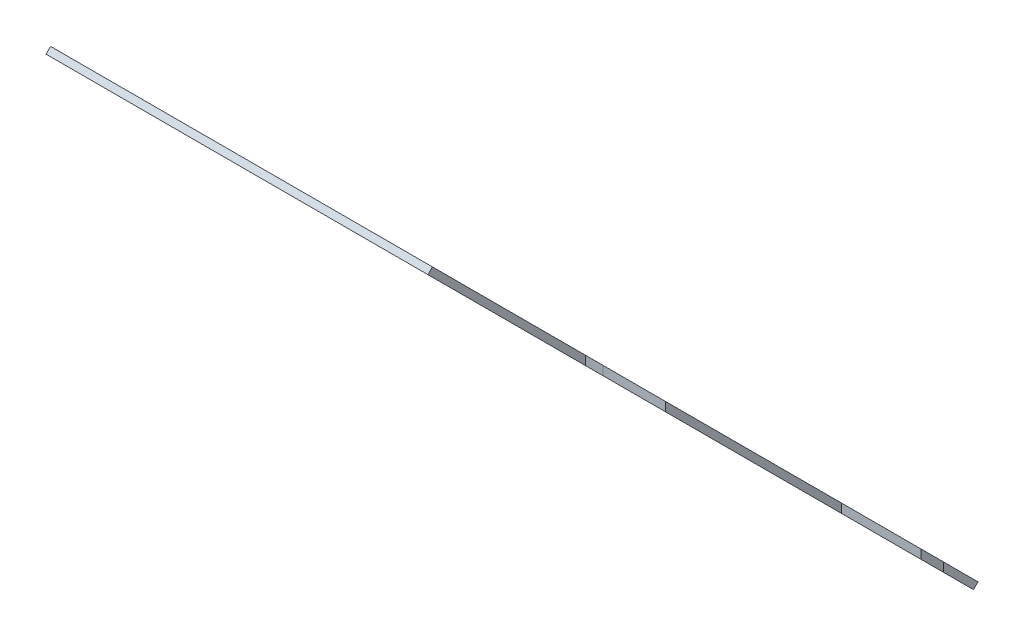
SolidWorks part; units mm, degrees
ref_plane "Plano frontal" through (0, 0, 0) normal (0, 0, 1) x (1, 0, 0)
ref_plane "Plano superior" through (0, 0, 0) normal (0, 1, 0) x (1, 0, 0)
ref_plane "Plano direito" through (0, 0, 0) normal (1, 0, 0) x (0, 0, -1)
sketch "Sketch3" plane through (0, 0, 0) normal (1, 0, 0) x (0, 0, -1)
  line L0 (-40199.9002, 3730.3647) -> (-40199.9002, 2810.9901) construction
  line L1 (-40199.9002, 12144.1489) -> (-40199.9002, -2855.8511) construction
  line L2 (-40199.9002, 2810.9901) -> (-41009.724, 3620.8139)
  line L3 (-41009.724, 3620.8139) -> (-41002.653, 3627.885)
  line L4 (-41002.653, 3627.885) -> (-40199.9002, 2825.1322)
  line L5 (-40199.9002, 2825.1322) -> (-40199.9002, 2810.9901)
  dimension "D1" = 10
  dimension "D2" = 45
extrude "Boss-Extrude1" add sketch "Sketch3" against normal blind 600 from surface at -22799.5611
sketch "Sketch4" plane through (0, 0, 0) normal (0, 1, 0) x (1, 0, 0)
  line L0 (-22799.5611, -40199.9002) -> (-22799.5611, -41002.653) construction
  line L1 (-22799.5611, -40360.1738) -> (-23030.5481, -40360.1738)
  line L2 (-22799.5611, -40360.1738) -> (-22799.5611, -40235.0266)
  line L3 (-22799.5611, -40235.0266) -> (-23030.5481, -40235.0266)
  line L5 (-22897.4106, -40699.3838) -> (-22959.9842, -40699.3838) construction
  line L6 (-22799.5611, -40761.9574) -> (-22897.4106, -40761.9574)
  line L7 (-22799.5611, -40761.9574) -> (-22799.5611, -40636.8102)
  line L8 (-22799.5611, -40636.8102) -> (-22897.4106, -40636.8102)
  line L10 (-23030.5481, -40297.6002) -> (-23093.1217, -40297.6002) construction
  line L11 (-22897.4106, -40761.9574) -> (-22897.4106, -40636.8102) construction
  line L12 (-23030.5481, -40360.1738) -> (-23030.5481, -40235.0266) construction
  line L13 (-22901.7025, -40699.3838) -> (-23026.1108, -40699.3838) construction
  arc A4 (-23030.5481, -40235.0266) -> (-23030.5481, -40360.1738) centre (-23030.5481, -40297.6002) ccw
  arc A5 (-22897.4106, -40636.8102) -> (-22897.4106, -40761.9574) centre (-22897.4106, -40699.3838) ccw
extrude "Cut-Extrude1" cut sketch "Sketch4" against normal up to vertex from vertex
sketch "Sketch5" plane through (-23399.5611, 0, 0) normal (-1, 0, 0) x (0, 0, 1)
  line L0 (40199.9002, 2810.9901) -> (40043.6383, 2654.7282)
  line L1 (40043.6383, 2654.7282) -> (40043.6383, 2668.8703)
  line L2 (40043.6383, 2668.8703) -> (40199.9002, 2825.1322)
  line L3 (40199.9002, 2825.1322) -> (40199.9002, 2810.9901)
  line L4 (40043.6383, 2668.8703) -> (40050.7093, 2661.7993)
  line M8 (40199.9002, 2825.1322) -> (40199.9002, 2810.9901)
extrude "Boss-Extrude2" add sketch "Sketch5" against normal up to surface (498 mm away) contours L2 L4 L0 M8
sketch "Sketch6" plane through (0, -18687.384, 18687.384) normal (0, 0.7071, -0.7071) x (1, 0, 0)
  line L0 (-23164.5611, -30416.8045) -> (-23359.5611, -30416.8045) construction
  line L1 (-23164.5611, -30426.8045) -> (-23359.5611, -30426.8045)
  line L2 (-23164.5611, -30406.8045) -> (-23359.5611, -30406.8045)
  line L3 (-23359.5611, -30416.8045) -> (-23359.5611, -31160.8045) construction
  line L4 (-23349.5611, -30416.8045) -> (-23349.5611, -31160.8045)
  line L5 (-23369.5611, -30416.8045) -> (-23369.5611, -31160.8045)
  line L6 (-23359.5611, -31160.8045) -> (-23039.5611, -31160.8045) construction
  line L7 (-23359.5611, -31150.8045) -> (-23039.5611, -31150.8045)
  line L8 (-23359.5611, -31170.8045) -> (-23039.5611, -31170.8045)
  line L9 (-23399.5611, -31558.5561) -> (-23399.5611, -30202.3045) construction
  line L11 (-23164.5611, -30596.8045) -> (-23359.5611, -30596.8045) construction
  line L12 (-23164.5611, -30606.8045) -> (-23359.5611, -30606.8045)
  line L13 (-23164.5611, -30586.8045) -> (-23359.5611, -30586.8045)
  line L14 (-23359.5611, -30980.8045) -> (-23039.5611, -30980.8045) construction
  line L15 (-23359.5611, -30970.8045) -> (-23039.5611, -30970.8045)
  line L16 (-23359.5611, -30990.8045) -> (-23039.5611, -30990.8045)
  line L17 (-22901.5611, -30202.3045) -> (-23399.5611, -30202.3045) construction
  arc A0 (-23164.5611, -30426.8045) -> (-23164.5611, -30406.8045) centre (-23164.5611, -30416.8045) ccw
  arc A1 (-23359.5611, -30406.8045) -> (-23359.5611, -30426.8045) centre (-23359.5611, -30416.8045) ccw
  arc A2 (-23349.5611, -30416.8045) -> (-23369.5611, -30416.8045) centre (-23359.5611, -30416.8045) ccw
  arc A3 (-23369.5611, -31160.8045) -> (-23349.5611, -31160.8045) centre (-23359.5611, -31160.8045) ccw
  arc A4 (-23359.5611, -31150.8045) -> (-23359.5611, -31170.8045) centre (-23359.5611, -31160.8045) ccw
  arc A5 (-23039.5611, -31170.8045) -> (-23039.5611, -31150.8045) centre (-23039.5611, -31160.8045) ccw
  arc A6 (-23164.5611, -30606.8045) -> (-23164.5611, -30586.8045) centre (-23164.5611, -30596.8045) ccw
  arc A7 (-23359.5611, -30586.8045) -> (-23359.5611, -30606.8045) centre (-23359.5611, -30596.8045) ccw
  arc A8 (-23359.5611, -30970.8045) -> (-23359.5611, -30990.8045) centre (-23359.5611, -30980.8045) ccw
  arc A9 (-23039.5611, -30990.8045) -> (-23039.5611, -30970.8045) centre (-23039.5611, -30980.8045) ccw
  point P2 (-23262.0611, -30416.8045)
  point P7 (-23359.5611, -30788.8045)
  point P14 (-23199.5611, -31160.8045)
  point P26 (-23199.5611, -30980.8045)
  point P29 (-23262.0611, -30596.8045)
  dimension "D1" = 10
  dimension "D2" = 180
  dimension "D3" = 40
  dimension "D4" = 394.5
  dimension "D5" = 958.5
  dimension "D8" = 180
  dimension "D9" = 320
  dimension "D10" = 195
  dimension "D6" = 2
  dimension "D7" = 2
extrude "Cut-Extrude2" cut sketch "Sketch6" against normal through all contours L8 A5 L7 L4 A3 | L7 A4 A3 L4 | L15 A9 L16 A8 | L13 A7 L12 A6 | L1 A1 L2 A0
sketch3d "3DSketch2"
  line L0 (-23039.5611, 3219.353, 40594.1209) -> (-23359.5611, 3219.353, 40594.1209) construction
  line L1 (-23039.5611, 3212.2819, 40601.192) -> (-23039.5611, 3219.353, 40594.1209) construction
  line L2 (-23359.5611, 2820.5447, 40195.3127) -> (-23359.5611, 3219.353, 40594.1209) construction
  line L3 (-23164.5611, 2820.5447, 40195.3127) -> (-23359.5611, 2820.5447, 40195.3127) construction
  line L4 (-23164.5611, 2813.4737, 40202.3838) -> (-23164.5611, 2820.5447, 40195.3127) construction
  line L5 (-23359.5611, 2813.4737, 40202.3838) -> (-23359.5611, 2820.5447, 40195.3127) construction
  line L6 (-23164.5611, 2820.5447, 40195.3127) -> (-23354.5611, 2820.5447, 40195.3127)
  line L7 (-23359.5611, 2824.0803, 40198.8482) -> (-23359.5611, 3215.8174, 40590.5854)
  line L8 (-23354.5611, 3219.353, 40594.1209) -> (-23039.5611, 3219.353, 40594.1209)
  line L9 (-23039.5611, 3219.353, 40594.1209) -> (-23164.5611, 2820.5447, 40195.3127) construction
  arc A0 (-23354.5611, 2820.5447, 40195.3127) -> (-23359.5611, 2824.0803, 40198.8482) centre (-23354.5611, 2824.0803, 40198.8482) ccw
  arc A1 (-23359.5611, 3215.8174, 40590.5854) -> (-23354.5611, 3219.353, 40594.1209) centre (-23354.5611, 3215.8174, 40590.5854) ccw
  point P14 (-23359.5611, 2820.5447, 40195.3127)
  point P16 (-23354.5611, 2827.6158, 40195.3127)
  point P19 (-23359.5611, 3219.353, 40594.1209)
  point P20 (-23354.5611, 3219.353, 40587.0498)
  dimension "D1" = 5
